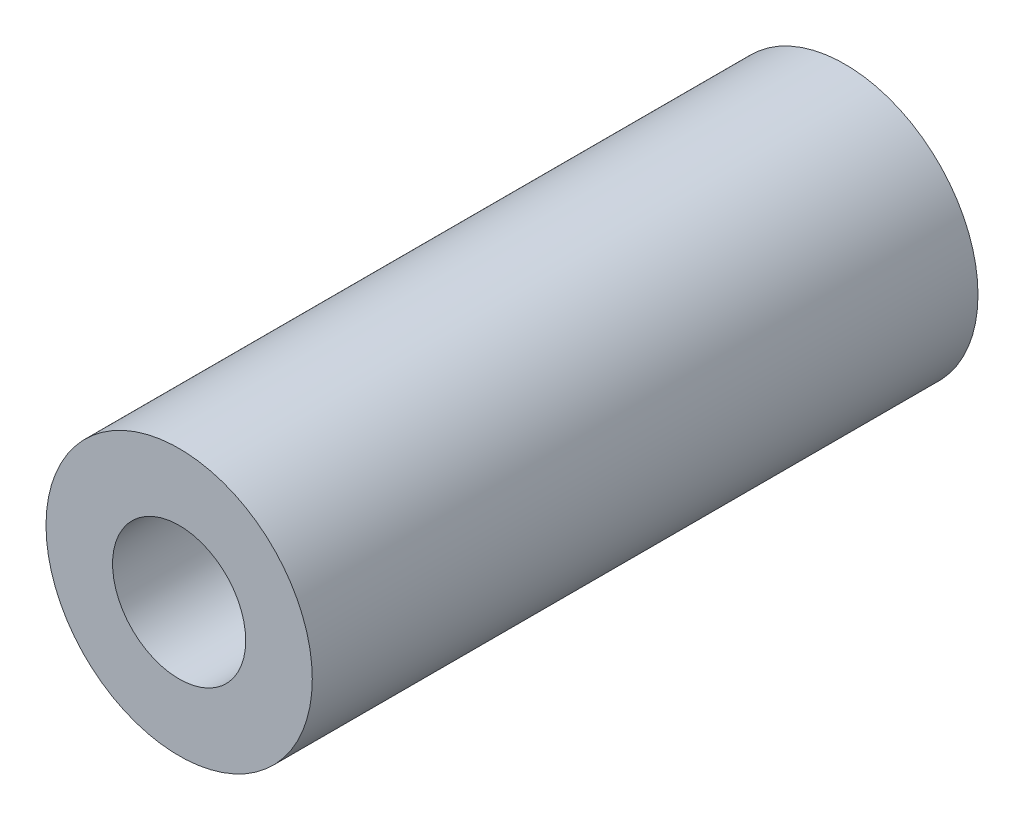
SolidWorks part; units mm, degrees
ref_plane "前视基准面" through (0, 0, 0) normal (0, 0, 1) x (1, 0, 0)
ref_plane "上视基准面" through (0, 0, 0) normal (0, 1, 0) x (1, 0, 0)
ref_plane "右视基准面" through (0, 0, 0) normal (1, 0, 0) x (0, 0, -1)
sketch "草图1" plane through (0, 0, 0) normal (0, 0, 1) x (1, 0, 0)
  circle A0 centre (0, 0) radius 4
  circle A1 centre (0, 0) radius 2
  dimension "D1" = 4
  dimension "D2" = 8
extrude "凸台-拉伸1" add sketch "草图1" along normal mid plane 20
